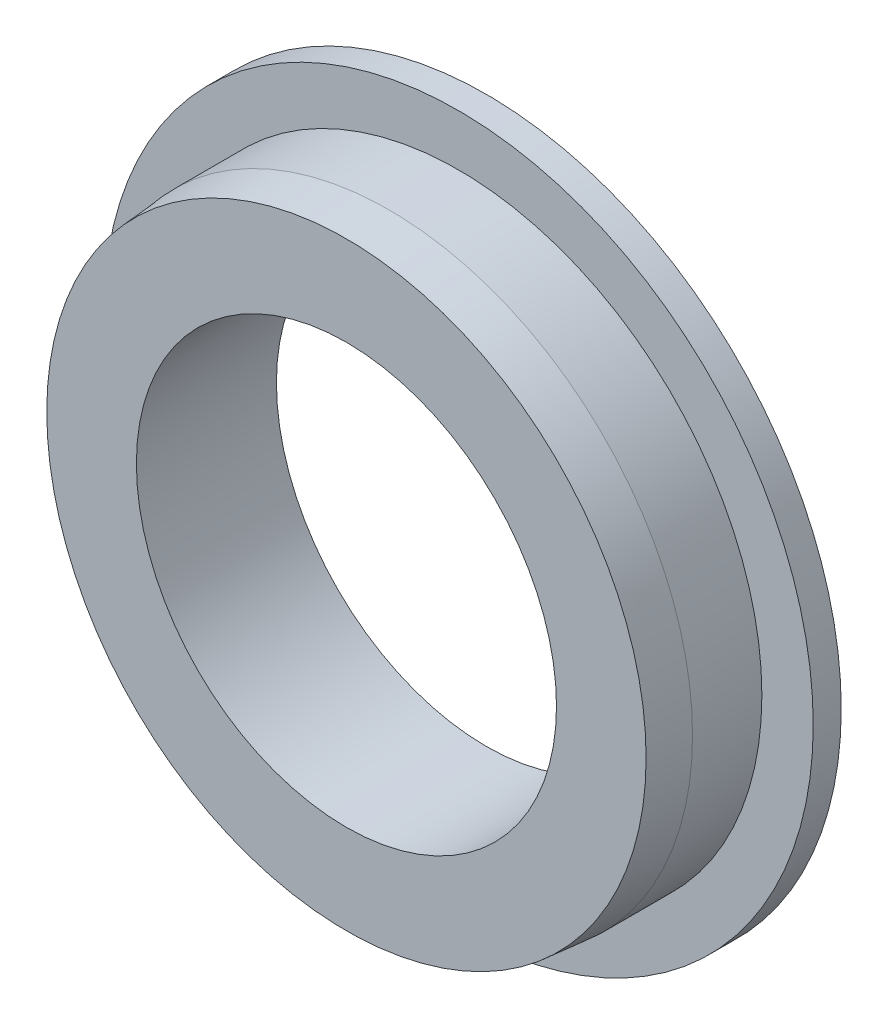
SolidWorks part; units mm, degrees
ref_plane "Front Plane" through (0, 0, 0) normal (0, 0, 1) x (1, 0, 0)
ref_plane "Top Plane" through (0, 0, 0) normal (0, 1, 0) x (1, 0, 0)
ref_plane "Right Plane" through (0, 0, 0) normal (1, 0, 0) x (0, 0, -1)
sketch "Sketch1" plane through (0, 0, 0) normal (0, 0, 1) x (1, 0, 0)
  circle A0 centre (0, 0) radius 24.13
  dimension "D1" = 48.26
extrude "Boss-Extrude1" add sketch "Sketch1" along normal mid plane 1.905
sketch "Sketch2" plane through (0, 0, 0.9525) normal (0, 0, 1) x (1, 0, 0)
  circle A0 centre (0, 0) radius 20.6375
  dimension "D1" = 41.275
extrude "Boss-Extrude2" add sketch "Sketch2" along normal blind 7.62
sketch "Sketch4" plane through (0, 0, -0.9525) normal (0, 0, -1) x (-1, 0, 0)
  circle A0 centre (0, 0) radius 14.2875
  dimension "D1" = 28.575
extrude "Cut-Extrude1" cut sketch "Sketch4" against normal through all
chamfer "Chamfer1" distance 0.254 angle 85 1 edges at (20.6375, 0, 8.5725)
